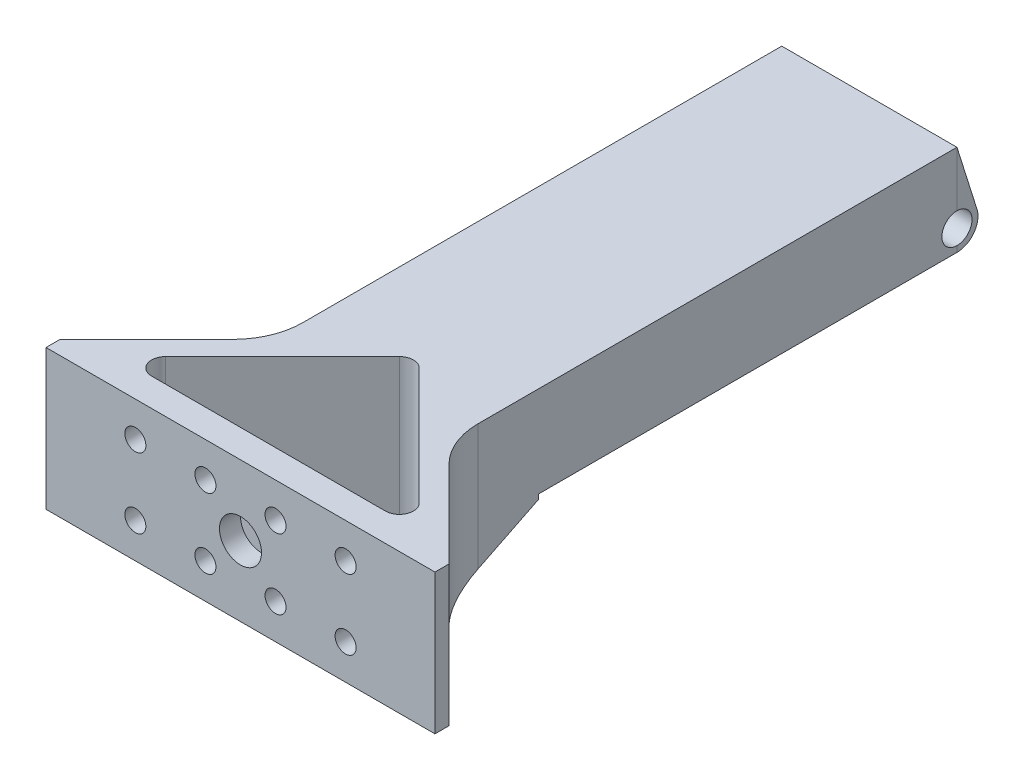
SolidWorks part; units mm, degrees
material "PLA"
ref_plane "정면" through (0, 0, 0) normal (0, 0, 1) x (1, 0, 0)
ref_plane "윗면" through (0, 0, 0) normal (0, 1, 0) x (1, 0, 0)
ref_plane "우측면" through (0, 0, 0) normal (1, 0, 0) x (0, 0, -1)
sketch "스케치1" plane through (0, 0, 0) normal (0, 1, 0) x (1, 0, 0)
  line L0 (27.75, 94.3974) -> (27.75, -27.5062) construction
  line L1 (40.2477, 89.7323) -> (15.2523, 89.7323)
  line L2 (0, 2) -> (0, 0)
  line L3 (15.2523, 17.2523) -> (0, 2)
  line L4 (40.2477, 89.7323) -> (40.2477, 17.2523)
  line L5 (40.2477, 17.2523) -> (55.5, 2)
  line L6 (55.5, 2) -> (55.5, 0)
  line L7 (55.5, 0) -> (0, 0)
  line L8 (15.2523, 89.7323) -> (15.2523, 17.2523)
  line L9 (11.0711, 4) -> (44.4289, 4)
  line L11 (45.8431, 7.4142) -> (29.1642, 24.0931)
  line L14 (9.6569, 7.4142) -> (26.3358, 24.0931)
  arc A0 (9.6569, 7.4142) -> (11.0711, 4) centre (11.0711, 6) ccw
  arc A1 (29.1642, 24.0931) -> (26.3358, 24.0931) centre (27.75, 22.6789) ccw
  arc A2 (44.4289, 4) -> (45.8431, 7.4142) centre (44.4289, 6) ccw
  point P12 (27.75, 89.7323)
  point P18 (27.75, 5)
  point P20 (27.75, 25.4481)
  dimension "D12" = 3
  dimension "D9" = 3
  dimension "D8" = 4
  dimension "D10" = 4
  dimension "D11" = 4
  dimension "D1" = 55.5
  dimension "D2" = 135
  dimension "D3" = 2
  dimension "D4" = 21.57
  dimension "D5" = 72.48
  dimension "D6" = 12.4977
  dimension "D7" = 4
extrude "보스-돌출1" add sketch "스케치1" along normal blind 20
sketch "스케치2" plane through (0, 0, 0) normal (0, 0, 1) x (1, 0, 0)
  line L0 (0, 20) -> (0, 0) construction
  line L1 (0, 20) -> (55.5, 20) construction
  line L2 (0, 10) -> (60.2338, 10) construction
  line L3 (27.75, 23.0111) -> (27.75, -4.7654) construction
  circle A0 centre (12.75, 15) radius 1.5
  circle A1 centre (22.75, 15) radius 1.5
  circle A2 centre (32.75, 15) radius 1.5
  circle A3 centre (42.75, 15) radius 1.5
  circle A4 centre (42.75, 5) radius 1.5
  circle A5 centre (32.75, 5) radius 1.5
  circle A6 centre (22.75, 5) radius 1.5
  circle A7 centre (12.75, 5) radius 1.5
  dimension "D1" = 12.75
  dimension "D3" = 10
  dimension "D4" = 3
  dimension "D5" = 3
  dimension "D2" = 5
extrude "컷-돌출1" cut sketch "스케치2" against normal blind 5
sketch "스케치3" plane through (0, 0, 0) normal (0, 0, 1) x (1, 0, 0)
  line L3 (55, 0) -> (-55, 0) construction
  line L4 (55.5, 20) -> (55.5, 0) construction
  circle A0 centre (27.75, 10) radius 3
  dimension "D1" = 6
  dimension "D2" = 10
  dimension "D3" = 27.75
extrude "컷-돌출2" cut sketch "스케치3" against normal blind 3
ref_plane "평면1" through (15.25, 0, 0) normal (1, 0, 0) x (0, 0, -1)
sketch "스케치4" plane through (0, 0, 0) normal (0, -1, 0) x (1, 0, 0)
  line L0 (15.25, -11) -> (15.25, 11) construction
  line L1 (40.2477, -89.7323) -> (15.25, -89.7323)
  line L2 (40.2477, -89.7323) -> (40.2477, -30.0023)
  line L3 (40.2477, -30.0023) -> (15.25, -30.0023)
  line L4 (15.25, -89.7323) -> (15.25, -30.0023)
  dimension "D1" = 59.73
extrude "컷-돌출3" cut sketch "스케치4" against normal blind 7
sketch "스케치5" plane through (15.2523, 0, 0) normal (-1, 0, 0) x (0, 0, 1)
  line L0 (-89.7323, 20) -> (-92.6247, 10.8041)
  line L1 (-89.7323, 20) -> (-89.7323, 7)
  line L2 (-30.0023, 7) -> (-89.7323, 7) construction
  arc A0 (-92.6247, 10.8041) -> (-89.7323, 7) centre (-89.7345, 10) ccw
  circle A1 centre (-89.7345, 10) radius 1.5
  line M8 (-89.7323, 20) -> (-89.7323, 7)
  dimension "D3" = 3
  dimension "D4" = 3
  dimension "D1" = 17.46
  dimension "D2" = 9.64
extrude "보스-돌출2" add sketch "스케치5" against normal blind 25 contours L1 A1 | A1 L0 A0 M8
sketch "스케치6" plane through (15.2523, 0, 0) normal (-1, 0, 0) x (0, 0, 1)
  circle A0 centre (-89.7345, 10) radius 2.15
  dimension "D1" = 4.3
extrude "컷-돌출4" cut sketch "스케치6" against normal through all
ref_plane "평면2" through (28, 0, 0) normal (1, 0, 0) x (0, 0, -1)
ref_plane "평면6" through (9.4585, -19.1033, -9.4585) normal (0.4056, -0.8192, -0.4056) x (-0.7071, 0, -0.7071)
sketch "스케치12" plane through (9.4585, -19.1033, -9.4585) normal (0.4056, -0.8192, -0.4056) x (-0.7071, 0, -0.7071)
  line L0 (-16.2602, 33.3056) -> (3.0481, 33.3056)
  line L1 (3.0481, 33.3056) -> (-6.6061, 45.2316)
  line L3 (-6.6061, 45.2316) -> (-16.2602, 33.3056)
extrude "컷-돌출9" cut sketch "스케치12" along normal blind 10
ref_plane "평면7" through (27.7477, 0, 0) normal (1, 0, 0) x (0, 0, -1)
mirror "대칭 복사2" about plane through (27.7477, 0, 0) normal (1, 0, 0) of "컷-돌출9"
fillet "필렛3" radius 10 1 edges at (27.7477, 0.0619, -29.8773)
sketch "스케치13" plane through (15.2523, 0, 0) normal (-1, 0, 0) x (0, 0, 1)
  circle A0 centre (-89.7345, 10) radius 2
  dimension "D1" = 4
sketch "스케치14" plane through (40.2477, 0, 0) normal (1, 0, 0) x (0, 0, -1)
  circle A0 centre (89.7345, 10) radius 2
fillet "필렛4" radius 10 2 edges at (15.2523, 10, -17.2523) (40.2477, 10, -17.2523)
